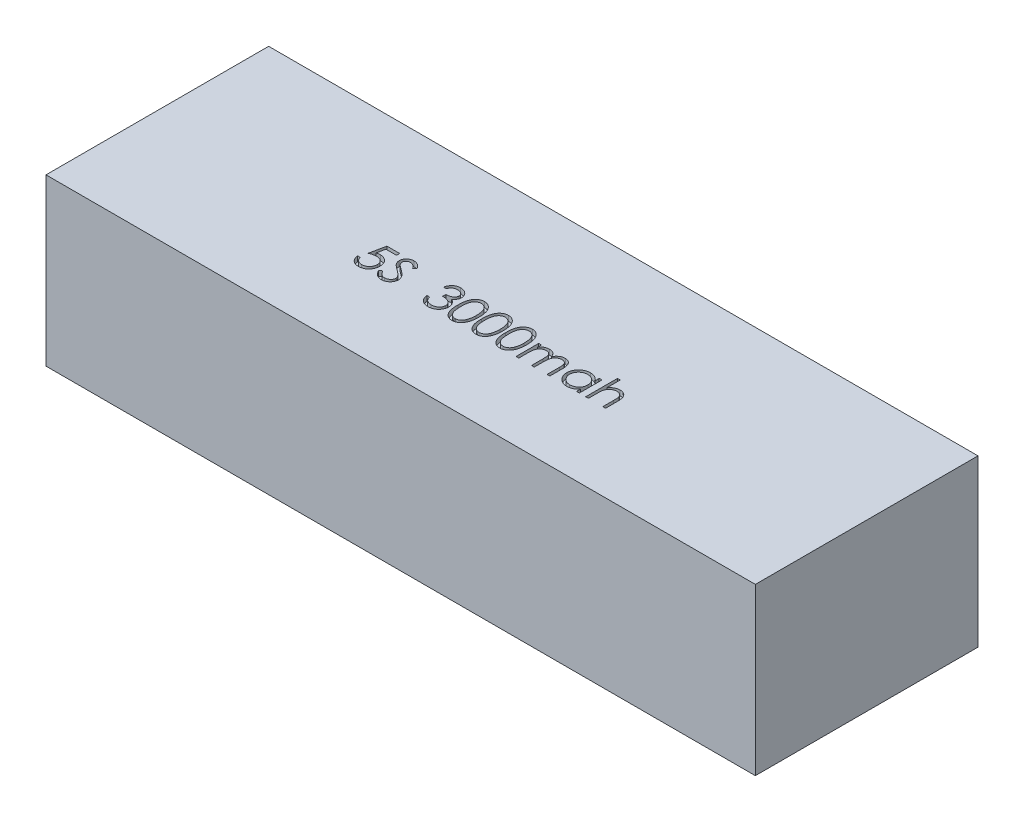
SolidWorks part; units mm, degrees
ref_plane "Front Plane" through (0, 0, 0) normal (0, 0, 1) x (1, 0, 0)
ref_plane "Top Plane" through (0, 0, 0) normal (0, 1, 0) x (1, 0, 0)
ref_plane "Right Plane" through (0, 0, 0) normal (1, 0, 0) x (0, 0, -1)
sketch "Sketch1" plane through (0, 0, 0) normal (0, 1, 0) x (1, 0, 0)
  line L1 (0, 0) -> (137, 0)
  line L2 (0, 0) -> (0, 43)
  line L3 (0, 43) -> (137, 43)
  line L4 (137, 0) -> (137, 43)
  dimension "D1" = 137
  dimension "D2" = 43
extrude "Boss-Extrude1" add sketch "Sketch1" along normal blind 32
sketch "Sketch2" plane through (0, 32, 0) normal (0, 1, 0) x (1, 0, 0)
  line L0 (0, 15) -> (137, 15) construction
  line L1 (0, 43) -> (0, 0) construction
  line L2 (137, 0) -> (137, 43) construction
  line L3 (0, 0) -> (137, 0) construction
  text T0 "5S  3000mah" font "Century Gothic" height 6
  point P6 (0, 12.4225)
  dimension "D1" = 15
extrude "Cut-Extrude1" cut sketch "Sketch2" against normal blind 1
